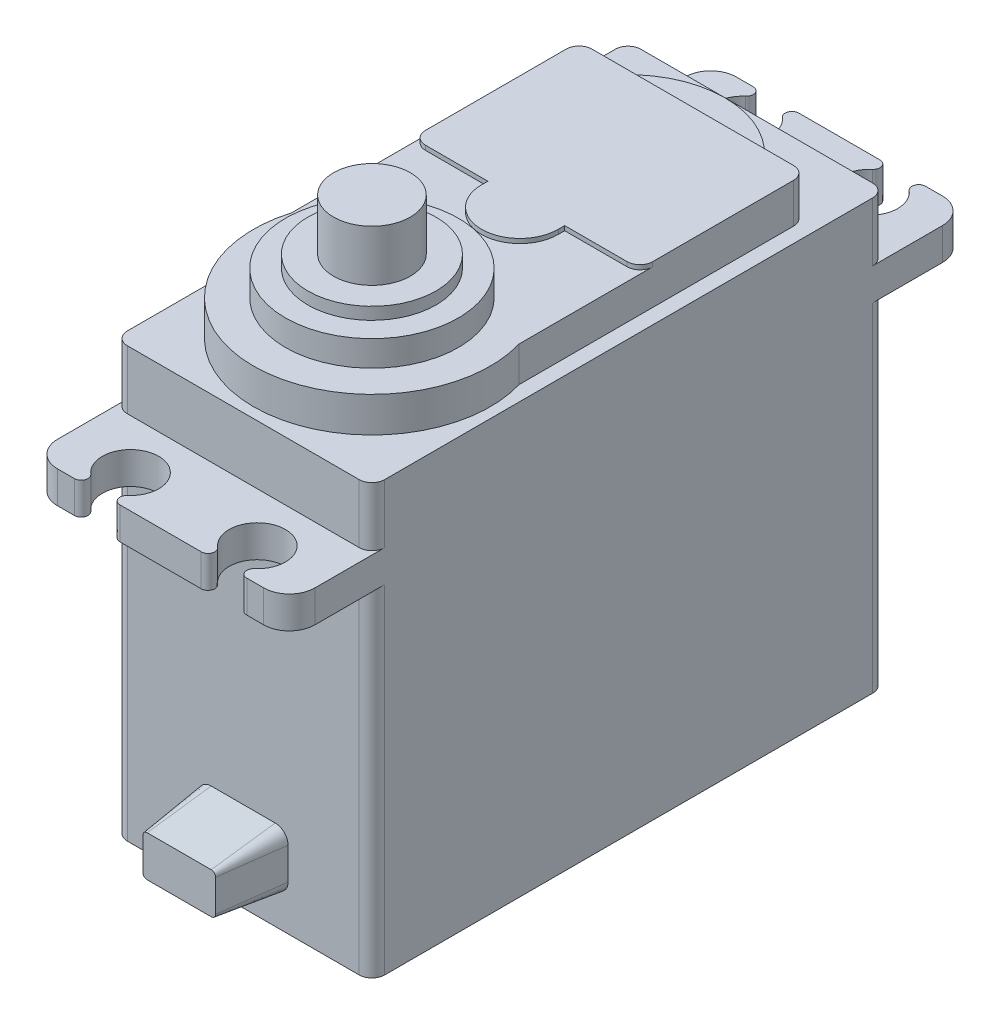
SolidWorks part; units mm, degrees
ref_plane "Front Plane" through (0, 0, 0) normal (0, 0, 1) x (1, 0, 0)
ref_plane "Top Plane" through (0, 0, 0) normal (0, 1, 0) x (1, 0, 0)
ref_plane "Right Plane" through (0, 0, 0) normal (1, 0, 0) x (0, 0, -1)
sketch "Sketch1" plane through (0, 0, 0) normal (1, 0, 0) x (0, 0, -1)
  line L0 (-20.05, 16.75) -> (20.05, 16.75)
  line L1 (20.05, 16.75) -> (20.05, 12.15)
  line L2 (20.05, 12.15) -> (26.5, 12.15)
  line L3 (26.5, 12.15) -> (26.5, 9.65)
  line L4 (26.5, 9.65) -> (20.05, 9.65)
  line L5 (20.05, 9.65) -> (20.05, -16.75)
  line L6 (20.05, -16.75) -> (-20.05, -16.75)
  line L7 (-20.05, -16.75) -> (-20.05, 9.65)
  line L8 (-20.05, 9.65) -> (-26.5, 9.65)
  line L9 (-26.5, 9.65) -> (-26.5, 12.15)
  line L10 (-26.5, 12.15) -> (-20.05, 12.15)
  line L11 (-20.05, 12.15) -> (-20.05, 16.75)
  line L12 (-20.05, 16.75) -> (20.05, -16.75) construction
  point P11 (20.6117, 6.0928)
  point P13 (19.9204, 6.6977)
  dimension "D1" = 40.1
  dimension "D2" = 33.5
  dimension "D3" = 2.5
  dimension "D4" = 26.4
  dimension "D5" = 53
extrude "Boss-Extrude1" add sketch "Sketch1" along normal mid plane 20.1
sketch "Sketch2" plane through (0, 16.75, 0) normal (0, 1, 0) x (1, 0, 0)
  line L0 (10.05, -26.5) -> (-10.05, -26.5) construction
  line L1 (0, 0) -> (0, -10) construction
  line L3 (-8.875, 15.05) -> (8.875, 15.05)
  line L4 (-8.875, 15.05) -> (-8.875, -7.3929)
  line L6 (8.875, 15.05) -> (8.875, -7.3929)
  line L7 (10.05, 20.05) -> (-10.05, 20.05) construction
  arc A0 (-8.875, -7.3929) -> (8.875, -7.3929) centre (0, -10) ccw
  arc A1 (8.875, -7.3929) -> (-8.875, -7.3929) centre (0, -10) ccw construction
  point P10 (0, 0)
  point P11 (0, 0)
  dimension "D1" = 16.5
  dimension "D2" = 9.25
  dimension "D3" = 17.75
  dimension "D4" = 5
extrude "Boss-Extrude2" add sketch "Sketch2" along normal blind 2.75
sketch "Sketch3" plane through (0, 16.75, 0) normal (0, 1, 0) x (1, 0, 0)
  line L0 (8.875, 15.05) -> (-8.875, 15.05) construction
  line L1 (0, 0) -> (0, 10.05) construction
  circle A0 centre (0, 10.05) radius 7.5
  dimension "D1" = 15
  dimension "D2" = 5
extrude "Boss-Extrude3" add sketch "Sketch3" along normal blind 2.5
sketch "Sketch4" plane through (0, 19.5, 0) normal (0, 1, 0) x (1, 0, 0)
  circle A0 centre (0, -10) radius 6.75
  arc A1 (-8.875, -7.3929) -> (8.875, -7.3929) centre (0, -10) ccw construction
  dimension "D1" = 13.5
extrude "Boss-Extrude4" add sketch "Sketch4" along normal blind 2
sketch "Sketch5" plane through (0, 21.5, 0) normal (0, 1, 0) x (1, 0, 0)
  circle A0 centre (0, -10) radius 5
  circle A1 centre (0, -10) radius 6.75 construction
  dimension "D1" = 10
extrude "Boss-Extrude5" add sketch "Sketch5" along normal offset from surface (0.95 mm away) 39.2 up to face at (0, -16.75, 0)
sketch "Sketch6" plane through (0, 22.45, 0) normal (0, 1, 0) x (1, 0, 0)
  circle A0 centre (0, -10) radius 3
  circle A1 centre (0, -10) radius 5 construction
  dimension "D1" = 6
extrude "Servo Spline" add sketch "Sketch6" along normal blind 4
fillet "Fillet1" radius 1 2 edges at (-8.875, 18.125, -15.05) (8.875, 18.125, -15.05)
sketch "Sketch7" plane through (0, 19.5, 0) normal (0, 1, 0) x (1, 0, 0)
  line L0 (-7.875, 2.05) -> (-3, 2.05)
  line L1 (-3, 1.55) -> (-3, 2.05)
  line L2 (3, 2.05) -> (7.875, 2.05)
  line L3 (7.875, 15.05) -> (-7.875, 15.05)
  line L4 (-8.875, 14.05) -> (-8.875, -7.3929)
  line L5 (8.875, -7.3929) -> (8.875, 14.05)
  line L6 (7.875, 15.05) -> (-7.875, 15.05)
  line L7 (-8.875, 14.05) -> (-8.875, 3.05)
  line L8 (8.875, 3.05) -> (8.875, 14.05)
  line L9 (3, 1.55) -> (3, 2.05)
  line L10 (0, 0) -> (0, 1.55) construction
  arc A0 (-3, 1.55) -> (3, 1.55) centre (0, 1.55) ccw
  arc A1 (7.875, 2.05) -> (8.875, 3.05) centre (7.875, 3.05) ccw
  arc A2 (-7.875, 2.05) -> (-8.875, 3.05) centre (-7.875, 3.05) cw
  arc A3 (-7.875, 15.05) -> (-8.875, 14.05) centre (-7.875, 14.05) ccw
  arc A4 (-8.875, -7.3929) -> (8.875, -7.3929) centre (0, -10) ccw
  arc A5 (8.875, 14.05) -> (7.875, 15.05) centre (7.875, 14.05) ccw
  arc A6 (-7.875, 15.05) -> (-8.875, 14.05) centre (-7.875, 14.05) ccw
  arc A8 (8.875, 14.05) -> (7.875, 15.05) centre (7.875, 14.05) ccw
  dimension "D2" = 6
  dimension "D5" = 1
  dimension "D3" = 13.5
  dimension "D4" = 13
  dimension "D1" = 0
extrude "Boss-Extrude7" add sketch "Sketch7" along normal blind 0.35
sketch "Sketch8" plane through (0, 12.15, 0) normal (0, 1, 0) x (1, 0, 0)
  line L0 (-4.95, -23.9) -> (4.95, -23.9) construction
  line L1 (4.95, -23.9) -> (4.95, 23.9) construction
  line L2 (4.95, 23.9) -> (-4.95, 23.9) construction
  line L3 (-4.95, 23.9) -> (-4.95, -23.9) construction
  line L4 (10.05, 26.5) -> (-10.05, 26.5) construction
  line L5 (0, 23.9) -> (0, 0) construction
  line L6 (0, 0) -> (0, -23.9) construction
  line L7 (10.05, -26.5) -> (-10.05, -26.5) construction
  line L8 (6.7301, -26.5) -> (3.1699, -26.5)
  line L9 (-6.2, -26.5) -> (-6.2, -25.4399) construction
  line L10 (-3.1699, -26.5) -> (-6.7301, -26.5)
  line L11 (-6.2, -25.4399) -> (-3.7, -25.4399) construction
  line L12 (-6.7301, 26.5) -> (-3.1699, 26.5)
  line L13 (-3.7, -25.4399) -> (-3.7, -26.5) construction
  line L14 (3.1699, 26.5) -> (6.7301, 26.5)
  arc A0 (-3.5155, -25.568) -> (-6.3845, -25.568) centre (-4.95, -23.9) ccw
  arc A1 (-6.3845, 25.568) -> (-3.5155, 25.568) centre (-4.95, 23.9) ccw
  arc A2 (3.5155, 25.568) -> (6.3845, 25.568) centre (4.95, 23.9) ccw
  arc A3 (6.3845, -25.568) -> (3.5155, -25.568) centre (4.95, -23.9) ccw
  arc A4 (-6.3845, 25.568) -> (-6.7301, 26.5) centre (-6.7301, 25.9699) ccw
  arc A5 (6.7301, 26.5) -> (6.3845, 25.568) centre (6.7301, 25.9699) ccw
  arc A6 (6.3845, -25.568) -> (6.7301, -26.5) centre (6.7301, -25.9699) ccw
  arc A7 (-6.7301, -26.5) -> (-6.3845, -25.568) centre (-6.7301, -25.9699) ccw
  arc A8 (-3.5155, -25.568) -> (-3.1699, -26.5) centre (-3.1699, -25.9699) ccw
  arc A9 (3.1699, -26.5) -> (3.5155, -25.568) centre (3.1699, -25.9699) ccw
  arc A10 (3.5155, 25.568) -> (3.1699, 26.5) centre (3.1699, 25.9699) ccw
  arc A11 (-3.1699, 26.5) -> (-3.5155, 25.568) centre (-3.1699, 25.9699) ccw
  dimension "D1" = 9.9
  dimension "D2" = 4.4
  dimension "D4" = 2.5
  dimension "D3" = 47.8
extrude "Cut-Extrude1" cut sketch "Sketch8" against normal through all
fillet "Fillet2" radius 2 4 edges at (-10.05, 10.9, -26.5) (10.05, 10.9, -26.5) (10.05, 10.9, 26.5) (-10.05, 10.9, 26.5)
fillet "Fillet3" radius 1 8 edges at (-10.05, -3.55, -20.05) (10.05, -3.55, -20.05) (10.05, -3.55, 20.05) (-10.05, -3.55, 20.05) (-10.05, 14.45, 20.05) (-10.05, 14.45, -20.05) (10.05, 14.45, -20.05) (10.05, 14.45, 20.05)
sketch "Sketch9" plane through (0, 0, 20.05) normal (0, 0, 1) x (1, 0, 0)
  line L0 (0, -12) -> (0, 0) construction
  line L1 (-2.5, -14.25) -> (2.5, -14.25)
  line L2 (-3.5, -13.25) -> (-3.5, -10.75)
  line L3 (-2.5, -9.75) -> (2.5, -9.75)
  line L4 (3.5, -13.25) -> (3.5, -10.75)
  line L5 (-3.5, -14.25) -> (3.5, -9.75) construction
  line L6 (-3.5, -9.75) -> (3.5, -14.25) construction
  line L7 (9.05, -16.75) -> (-9.05, -16.75) construction
  arc A0 (-2.5, -14.25) -> (-3.5, -13.25) centre (-2.5, -13.25) cw
  arc A1 (2.5, -14.25) -> (3.5, -13.25) centre (2.5, -13.25) ccw
  arc A2 (2.5, -9.75) -> (3.5, -10.75) centre (2.5, -10.75) cw
  arc A3 (-3.5, -10.75) -> (-2.5, -9.75) centre (-2.5, -10.75) cw
  point P0 (0, -12)
  dimension "D4" = 1
  dimension "D1" = 7
  dimension "D2" = 4.5
  dimension "D3" = 2.5
extrude "Boss-Extrude8" add sketch "Sketch9" along normal blind 5 draft 7.5
